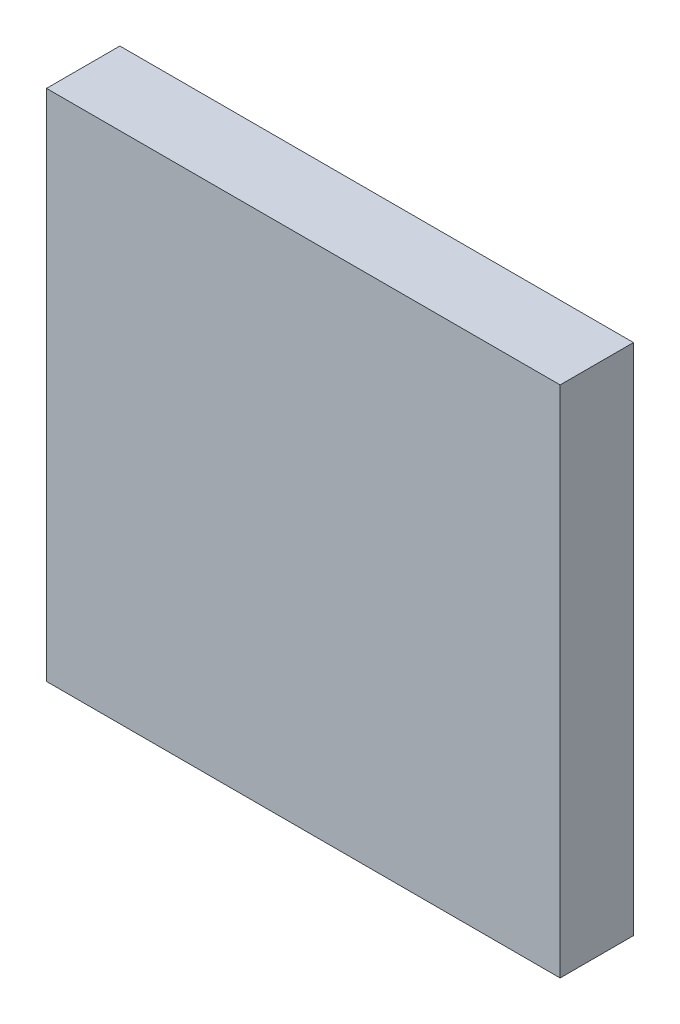
SolidWorks part; units mm, degrees
ref_plane "Plan de face" through (0, 0, 0) normal (0, 0, 1) x (1, 0, 0)
ref_plane "Plan de dessus" through (0, 0, 0) normal (0, 1, 0) x (1, 0, 0)
ref_plane "Plan de droite" through (0, 0, 0) normal (1, 0, 0) x (0, 0, -1)
sketch "Esquisse1" plane through (0, 0, 0) normal (0, 0, 1) x (1, 0, 0)
  line L1 (-3.5, -3.5) -> (3.5, -3.5)
  line L2 (-3.5, -3.5) -> (-3.5, 3.5)
  line L3 (-3.5, 3.5) -> (3.5, 3.5)
  line L4 (3.5, -3.5) -> (3.5, 3.5)
  line L5 (-3.5, -3.5) -> (3.5, 3.5) construction
  line L6 (-3.5, 3.5) -> (3.5, -3.5) construction
  point P0 (0, 0)
  dimension "D1" = 7
  dimension "D2" = 7
extrude "Boss.-Extru.1" add sketch "Esquisse1" along normal blind 1
